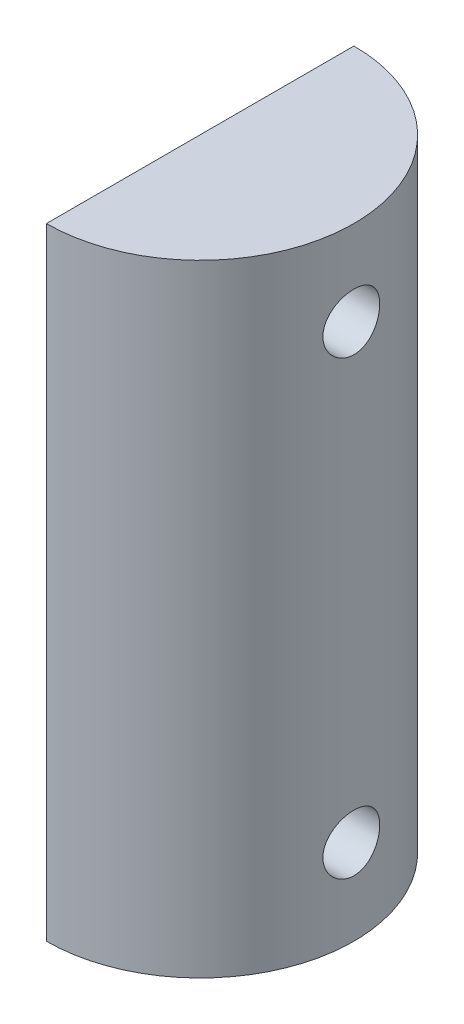
SolidWorks part; units mm, degrees
ref_plane "Front Plane" through (0, 0, 0) normal (0, 0, 1) x (1, 0, 0)
ref_plane "Top Plane" through (0, 0, 0) normal (0, 1, 0) x (1, 0, 0)
ref_plane "Right Plane" through (0, 0, 0) normal (1, 0, 0) x (0, 0, -1)
sketch "Sketch1" plane through (0, 0, 0) normal (0, 1, 0) x (1, 0, 0)
  line L0 (0, 32.5) -> (0, -32.5) construction
  circle A0 centre (0, 0) radius 32.5
  dimension "D1" = 65
extrude "Boss-Extrude2" add sketch "Sketch1" against normal blind 131.3737 contours A0 L0
sketch "Sketch2" plane through (0, 0, 0) normal (-1, 0, 0) x (0, 0, 1)
  line L0 (0, 0) -> (0, -18) construction
  line L1 (0, -131.3737) -> (0, -113.3737) construction
  line L2 (-32.5, -131.3737) -> (32.5, -131.3737) construction
  circle A0 centre (0, -18) radius 6
  circle A1 centre (0, -113.3737) radius 6
  dimension "D3" = 12
  dimension "D4" = 12
  dimension "D1" = 18
  dimension "D2" = 18
extrude "Cut-Extrude1" cut sketch "Sketch2" against normal blind 59
